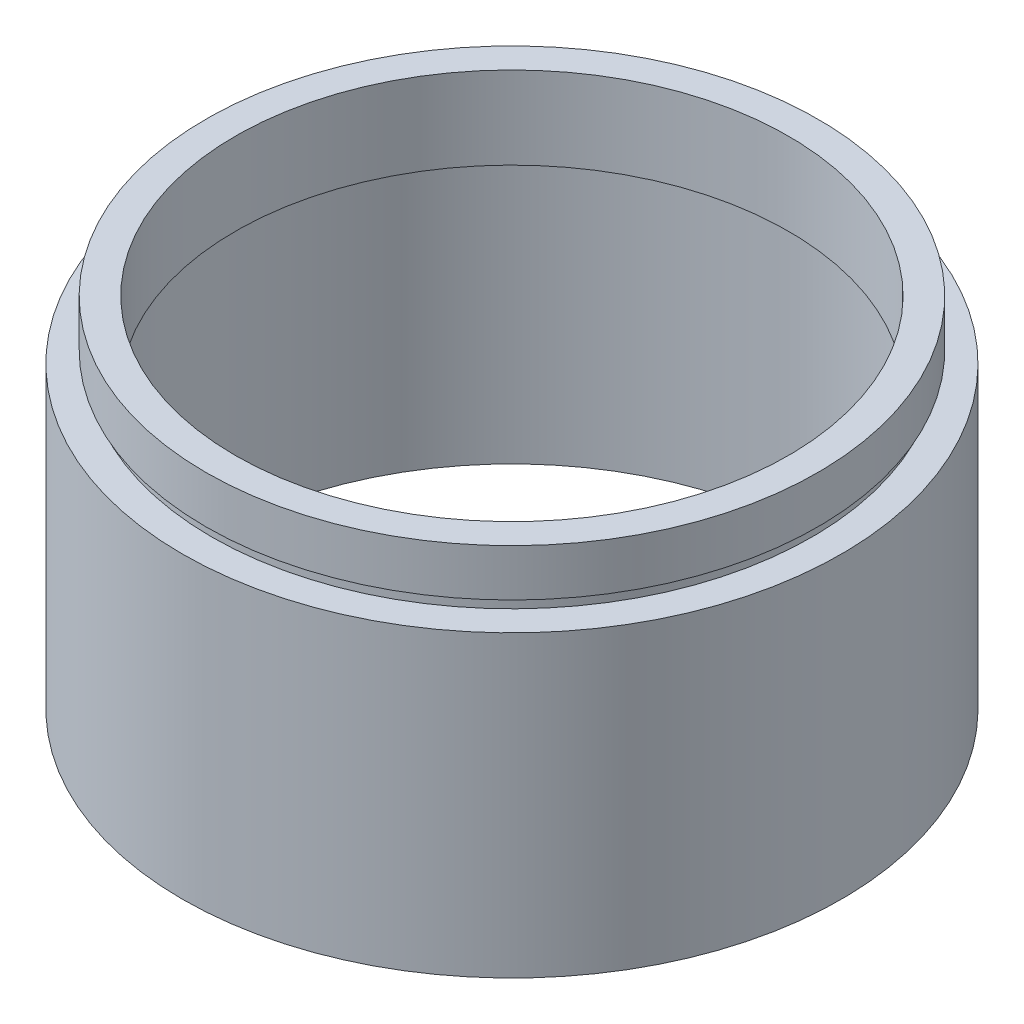
SolidWorks part; units mm, degrees
ref_plane "前视基准面" through (0, 0, 0) normal (0, 0, 1) x (1, 0, 0)
ref_plane "上视基准面" through (0, 0, 0) normal (0, 1, 0) x (1, 0, 0)
ref_plane "右视基准面" through (0, 0, 0) normal (1, 0, 0) x (0, 0, -1)
sketch "草图1" plane through (0, 0, 0) normal (0, 0, 1) x (1, 0, 0)
  line L0 (0, 161.3762) -> (0, 0) construction
  line L1 (141.7365, 0) -> (-131.7984, 0) construction
  line L2 (23.5, 30.4) -> (26, 30.4)
  line L3 (26, 30.4) -> (26, 26.4)
  line L4 (26, 26.4) -> (25.5, 26.4)
  line L5 (25.5, 26.4) -> (25.5, 25.4)
  line L6 (25.5, 25.4) -> (28, 25.4)
  line L7 (28, 25.4) -> (28, 0)
  line L8 (28, 0) -> (25.5, 0)
  line L9 (25.5, 0) -> (25.5, 22.4)
  line L10 (25.5, 22.4) -> (26.1, 22.4)
  line L11 (26.1, 22.4) -> (26.1, 23.4)
  line L12 (26.1, 23.4) -> (23.5, 23.4)
  line L13 (23.5, 23.4) -> (23.5, 30.4)
  dimension "D1" = 23.5
  dimension "D2" = 26
  dimension "D3" = 1
  dimension "D4" = 1
  dimension "D5" = 25.5
  dimension "D6" = 26.1
  dimension "D7" = 25.5
  dimension "D8" = 5
  dimension "D9" = 7
  dimension "D10" = 25.4
  dimension "D11" = 28
revolve "旋转1" add sketch "草图1" angle 360 about L0
cosmetic thread "装饰螺纹线1" parameters "D2"=52
cosmetic thread "装饰螺纹线2" parameters "D2"=48
cosmetic thread "装饰螺纹线3" parameters "D2"=51
